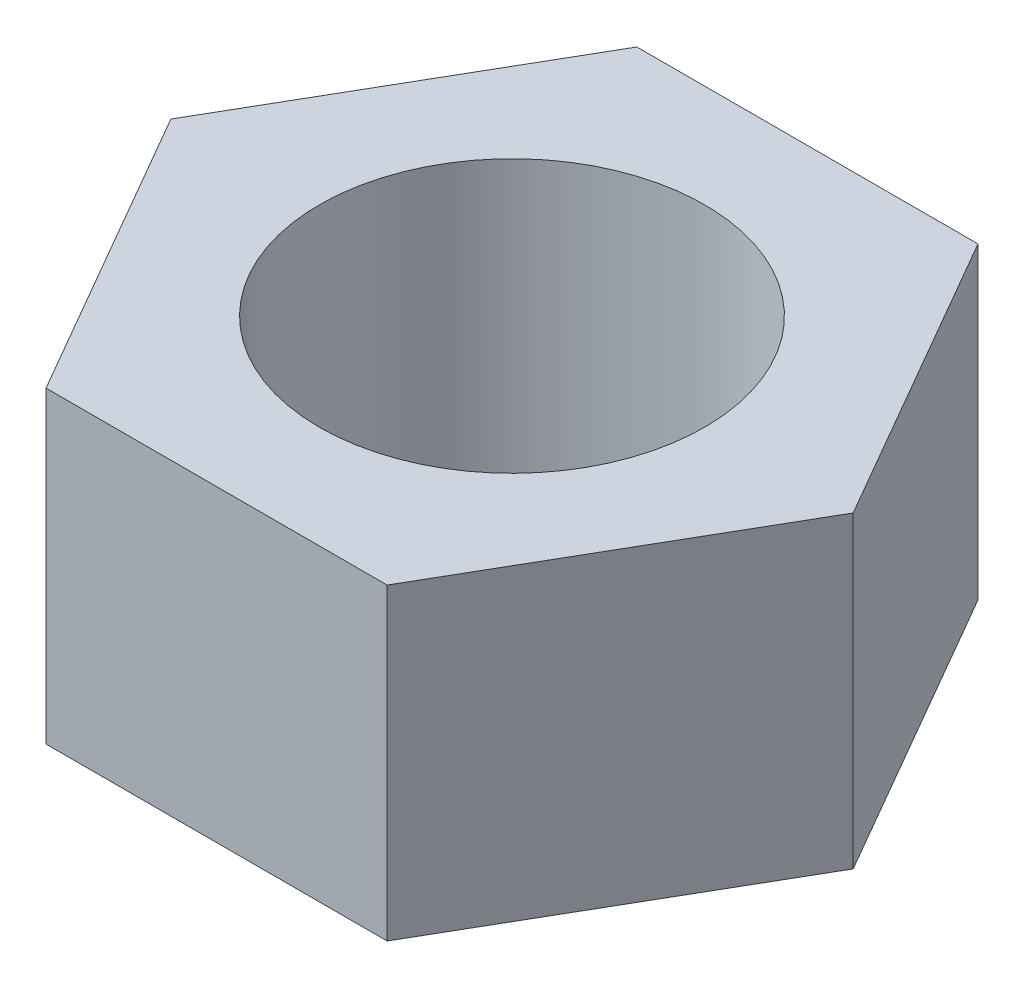
SolidWorks part; units mm, degrees
ref_plane "Front Plane" through (0, 0, 0) normal (0, 0, 1) x (1, 0, 0)
ref_plane "Top Plane" through (0, 0, 0) normal (0, 1, 0) x (1, 0, 0)
ref_plane "Right Plane" through (0, 0, 0) normal (1, 0, 0) x (0, 0, -1)
sketch "Sketch1" plane through (0, 0, 0) normal (0, 1, 0) x (1, 0, 0)
  line L1 (26.5581, 0) -> (13.2791, 23)
  line L2 (13.2791, 23) -> (-13.2791, 23)
  line L3 (-13.2791, 23) -> (-26.5581, 0)
  line L4 (-26.5581, 0) -> (-13.2791, -23)
  line L5 (-13.2791, -23) -> (13.2791, -23)
  line L6 (13.2791, -23) -> (26.5581, 0)
  circle A0 centre (0, 0) radius 23 construction
  dimension "D1" = 46
extrude "Boss-Extrude1" add sketch "Sketch1" along normal blind 24
sketch "Sketch2" plane through (0, 24, 0) normal (0, 1, 0) x (1, 0, 0)
  circle A0 centre (0, 0) radius 15
extrude "Cut-Extrude1" cut sketch "Sketch2" against normal through all
